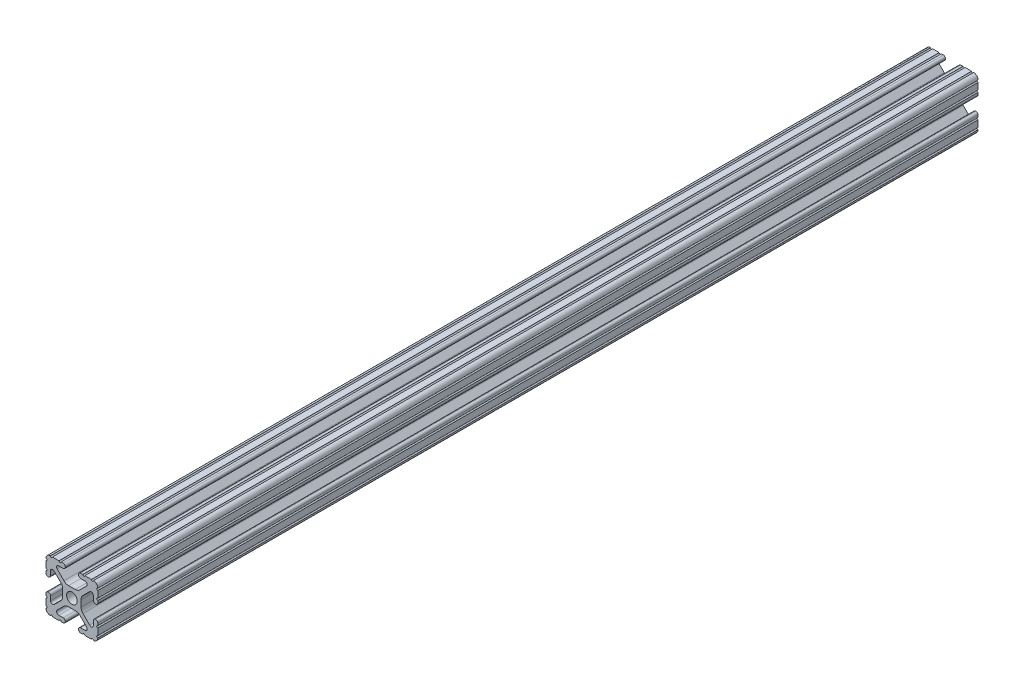
SolidWorks part; units mm, degrees
ref_plane "Front Plane" through (0, 0, 0) normal (0, 0, 1) x (1, 0, 0)
ref_plane "Top Plane" through (0, 0, 0) normal (0, 1, 0) x (1, 0, 0)
ref_plane "Right Plane" through (0, 0, 0) normal (1, 0, 0) x (0, 0, -1)
sketch "Sketch1" plane through (0, 0, 0) normal (0, 0, 1) x (1, 0, 0)
  line L88 (-7.1797, -8.6452) -> (-3.9523, -5.4237)
  line L89 (-1.7093, -4.4958) -> (1.7093, -4.4958)
  line L90 (3.9523, -5.4237) -> (7.1797, -8.6452)
  line L91 (6.4164, -10.4902) -> (4.2875, -10.4902)
  line L92 (3.2385, -11.5392) -> (3.2385, -11.651)
  line L93 (4.2875, -12.7) -> (5.3171, -12.7)
  line L94 (6.3331, -12.7) -> (9.5504, -12.7)
  line L95 (12.7, -9.5504) -> (12.7, -6.3331)
  line L96 (12.7, -5.3171) -> (12.7, -4.2875)
  line L97 (11.651, -3.2385) -> (11.5392, -3.2385)
  line L98 (10.4902, -4.2875) -> (10.4902, -6.4021)
  line L99 (8.7371, -7.1294) -> (5.441, -3.8408)
  line L100 (4.5085, -1.5932) -> (4.5085, 1.5932)
  line L101 (5.441, 3.8408) -> (8.7371, 7.1294)
  line L102 (10.4902, 6.4021) -> (10.4902, 4.2875)
  line L103 (11.5392, 3.2385) -> (11.651, 3.2385)
  line L104 (12.7, 4.2875) -> (12.7, 5.3171)
  line L105 (12.7, 6.3331) -> (12.7, 9.5504)
  line L106 (9.5504, 12.7) -> (6.3331, 12.7)
  line L107 (5.3171, 12.7) -> (4.2875, 12.7)
  line L108 (3.2385, 11.651) -> (3.2385, 11.5392)
  line L109 (4.2875, 10.4902) -> (6.4768, 10.4902)
  line L110 (7.207, 8.7244) -> (3.8983, 5.4232)
  line L111 (1.6558, 4.4958) -> (-1.6558, 4.4958)
  line L112 (-3.8983, 5.4232) -> (-7.207, 8.7244)
  line L113 (-6.4768, 10.4902) -> (-4.2875, 10.4902)
  line L114 (-3.2385, 11.5392) -> (-3.2385, 11.651)
  line L115 (-4.2875, 12.7) -> (-5.3171, 12.7)
  line L116 (-6.3331, 12.7) -> (-9.5504, 12.7)
  line L117 (-12.7, 9.5504) -> (-12.7, 6.3331)
  line L118 (-12.7, 5.3171) -> (-12.7, 4.2875)
  line L119 (-11.651, 3.2385) -> (-11.5392, 3.2385)
  line L120 (-10.4902, 4.2875) -> (-10.4902, 6.4021)
  line L121 (-8.7371, 7.1294) -> (-5.441, 3.8408)
  line L122 (-4.5085, 1.5932) -> (-4.5085, -1.5932)
  line L123 (-5.441, -3.8408) -> (-8.7371, -7.1294)
  line L124 (-10.4902, -6.4021) -> (-10.4902, -4.2875)
  line L125 (-11.5392, -3.2385) -> (-11.651, -3.2385)
  line L126 (-12.7, -4.2875) -> (-12.7, -5.3171)
  line L127 (-12.7, -6.3331) -> (-12.7, -9.5504)
  line L128 (-9.5504, -12.7) -> (-6.3331, -12.7)
  line L129 (-5.3171, -12.7) -> (-4.2875, -12.7)
  line L130 (-3.2385, -11.651) -> (-3.2385, -11.5392)
  line L131 (-4.2875, -10.4902) -> (-6.4164, -10.4902)
  circle A1 centre (0, 0) radius 2.6035
  arc A104 (-7.1797, -8.6452) -> (-6.4164, -10.4902) centre (-6.4164, -9.4098) ccw
  arc A105 (-1.7093, -4.4958) -> (-3.9523, -5.4237) centre (-1.7093, -7.6708) ccw
  arc A106 (3.9523, -5.4237) -> (1.7093, -4.4958) centre (1.7093, -7.6708) ccw
  arc A107 (6.4164, -10.4902) -> (7.1797, -8.6452) centre (6.4164, -9.4098) ccw
  arc A108 (4.2875, -10.4902) -> (3.2385, -11.5392) centre (4.2875, -11.5392) ccw
  arc A109 (3.2385, -11.651) -> (4.2875, -12.7) centre (4.2875, -11.651) ccw
  arc A110 (6.3331, -12.7) -> (5.3171, -12.7) centre (5.8251, -12.7) ccw
  arc A111 (10.5664, -12.6998) -> (9.5504, -12.7) centre (10.0584, -12.7) ccw
  arc A112 (10.5664, -12.6998) -> (12.6998, -10.5664) centre (10.5918, -10.5918) ccw
  arc A113 (12.7, -9.5504) -> (12.6998, -10.5664) centre (12.7, -10.0584) ccw
  arc A114 (12.7, -5.3171) -> (12.7, -6.3331) centre (12.7, -5.8251) ccw
  arc A115 (12.7, -4.2875) -> (11.651, -3.2385) centre (11.651, -4.2875) ccw
  arc A116 (11.5392, -3.2385) -> (10.4902, -4.2875) centre (11.5392, -4.2875) ccw
  arc A117 (8.7371, -7.1294) -> (10.4902, -6.4021) centre (9.4628, -6.4021) ccw
  arc A118 (4.5085, -1.5932) -> (5.441, -3.8408) centre (7.6835, -1.5932) ccw
  arc A119 (5.441, 3.8408) -> (4.5085, 1.5932) centre (7.6835, 1.5932) ccw
  arc A120 (10.4902, 6.4021) -> (8.7371, 7.1294) centre (9.4628, 6.4021) ccw
  arc A121 (10.4902, 4.2875) -> (11.5392, 3.2385) centre (11.5392, 4.2875) ccw
  arc A122 (11.651, 3.2385) -> (12.7, 4.2875) centre (11.651, 4.2875) ccw
  arc A123 (12.7, 6.3331) -> (12.7, 5.3171) centre (12.7, 5.8251) ccw
  arc A124 (12.6998, 10.5664) -> (12.7, 9.5504) centre (12.7, 10.0584) ccw
  arc A125 (12.6998, 10.5664) -> (10.5664, 12.6998) centre (10.5918, 10.5918) ccw
  arc A126 (9.5504, 12.7) -> (10.5664, 12.6998) centre (10.0584, 12.7) ccw
  arc A127 (5.3171, 12.7) -> (6.3331, 12.7) centre (5.8251, 12.7) ccw
  arc A128 (4.2875, 12.7) -> (3.2385, 11.651) centre (4.2875, 11.651) ccw
  arc A129 (3.2385, 11.5392) -> (4.2875, 10.4902) centre (4.2875, 11.5392) ccw
  arc A130 (7.207, 8.7244) -> (6.4768, 10.4902) centre (6.4768, 9.4563) ccw
  arc A131 (1.6558, 4.4958) -> (3.8983, 5.4232) centre (1.6558, 7.6708) ccw
  arc A132 (-3.8983, 5.4232) -> (-1.6558, 4.4958) centre (-1.6558, 7.6708) ccw
  arc A133 (-6.4768, 10.4902) -> (-7.207, 8.7244) centre (-6.4768, 9.4563) ccw
  arc A134 (-4.2875, 10.4902) -> (-3.2385, 11.5392) centre (-4.2875, 11.5392) ccw
  arc A135 (-3.2385, 11.651) -> (-4.2875, 12.7) centre (-4.2875, 11.651) ccw
  arc A136 (-6.3331, 12.7) -> (-5.3171, 12.7) centre (-5.8251, 12.7) ccw
  arc A137 (-10.5664, 12.6998) -> (-9.5504, 12.7) centre (-10.0584, 12.7) ccw
  arc A138 (-10.5664, 12.6998) -> (-12.6998, 10.5664) centre (-10.5918, 10.5918) ccw
  arc A139 (-12.7, 9.5504) -> (-12.6998, 10.5664) centre (-12.7, 10.0584) ccw
  arc A140 (-12.7, 5.3171) -> (-12.7, 6.3331) centre (-12.7, 5.8251) ccw
  arc A141 (-12.7, 4.2875) -> (-11.651, 3.2385) centre (-11.651, 4.2875) ccw
  arc A142 (-11.5392, 3.2385) -> (-10.4902, 4.2875) centre (-11.5392, 4.2875) ccw
  arc A143 (-8.7371, 7.1294) -> (-10.4902, 6.4021) centre (-9.4628, 6.4021) ccw
  arc A144 (-4.5085, 1.5932) -> (-5.441, 3.8408) centre (-7.6835, 1.5932) ccw
  arc A145 (-5.441, -3.8408) -> (-4.5085, -1.5932) centre (-7.6835, -1.5932) ccw
  arc A146 (-10.4902, -6.4021) -> (-8.7371, -7.1294) centre (-9.4628, -6.4021) ccw
  arc A147 (-10.4902, -4.2875) -> (-11.5392, -3.2385) centre (-11.5392, -4.2875) ccw
  arc A148 (-11.651, -3.2385) -> (-12.7, -4.2875) centre (-11.651, -4.2875) ccw
  arc A149 (-12.7, -6.3331) -> (-12.7, -5.3171) centre (-12.7, -5.8251) ccw
  arc A150 (-12.6998, -10.5664) -> (-12.7, -9.5504) centre (-12.7, -10.0584) ccw
  arc A151 (-12.6998, -10.5664) -> (-10.5664, -12.6998) centre (-10.5918, -10.5918) ccw
  arc A152 (-9.5504, -12.7) -> (-10.5664, -12.6998) centre (-10.0584, -12.7) ccw
  arc A153 (-5.3171, -12.7) -> (-6.3331, -12.7) centre (-5.8251, -12.7) ccw
  arc A154 (-4.2875, -12.7) -> (-3.2385, -11.651) centre (-4.2875, -11.651) ccw
  arc A155 (-3.2385, -11.5392) -> (-4.2875, -10.4902) centre (-4.2875, -11.5392) ccw
extrude "Boss-Extrude1" add sketch "Sketch1" along normal mid plane 431.8
